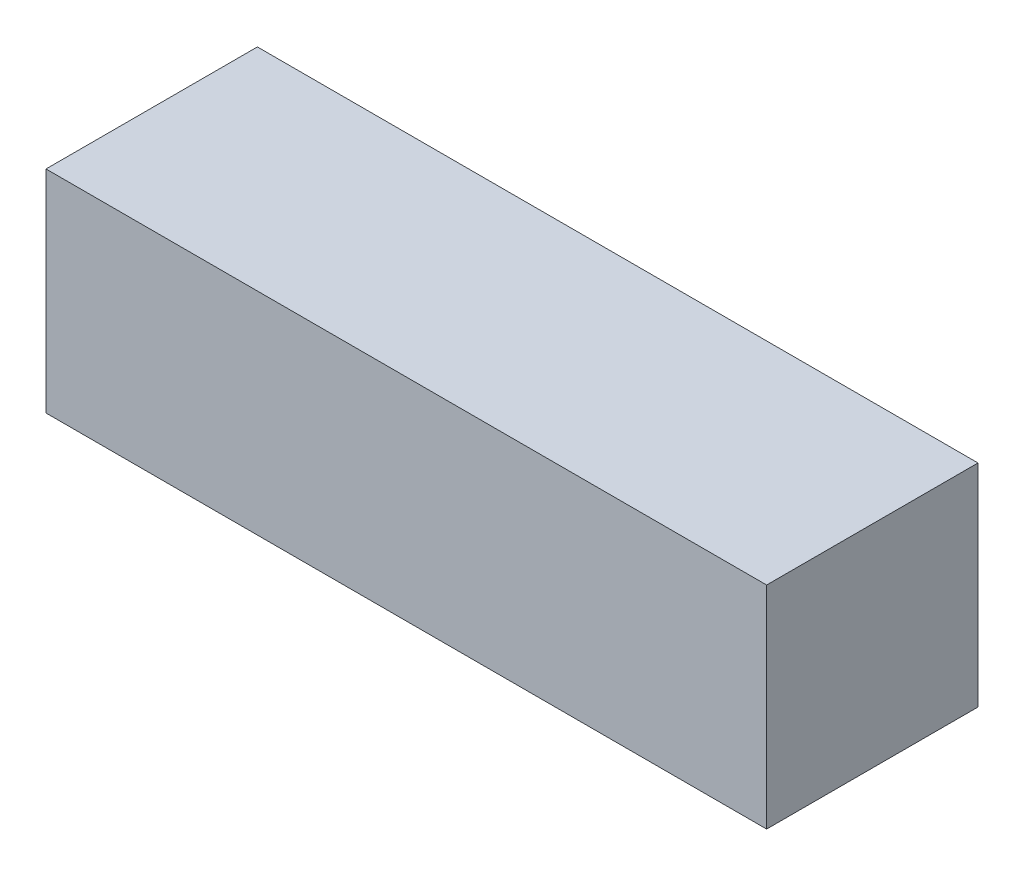
SolidWorks part; units mm, degrees
ref_plane "Front Plane" through (0, 0, 0) normal (0, 0, 1) x (1, 0, 0)
ref_plane "Top Plane" through (0, 0, 0) normal (0, 1, 0) x (1, 0, 0)
ref_plane "Right Plane" through (0, 0, 0) normal (1, 0, 0) x (0, 0, -1)
sketch "Sketch1" plane through (0, 0, 0) normal (0, 1, 0) x (1, 0, 0)
  line L1 (0, 0) -> (38.1, 0)
  line L2 (0, 0) -> (0, 11.176)
  line L3 (0, 11.176) -> (38.1, 11.176)
  line L4 (38.1, 0) -> (38.1, 11.176)
  dimension "D1" = 11.176
  dimension "D2" = 38.1
extrude "Boss-Extrude1" add sketch "Sketch1" along normal blind 11.176
